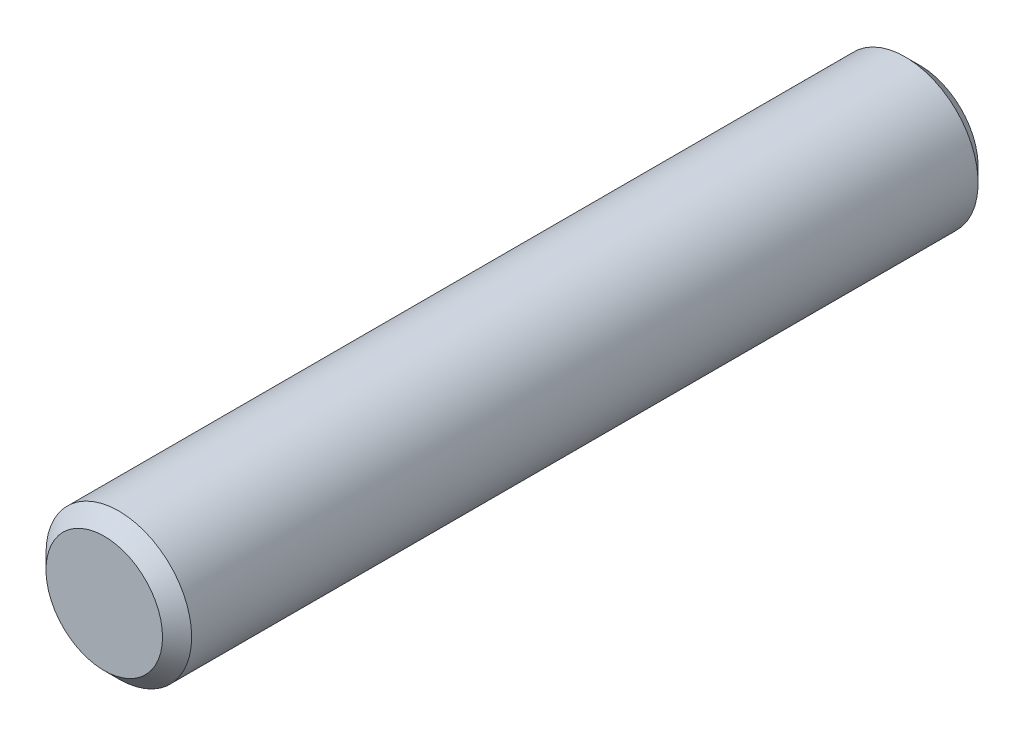
SolidWorks part; units mm, degrees
ref_plane "Plano frontal" through (0, 0, 0) normal (0, 0, 1) x (1, 0, 0)
ref_plane "Plano superior" through (0, 0, 0) normal (0, 1, 0) x (1, 0, 0)
ref_plane "Plano direito" through (0, 0, 0) normal (1, 0, 0) x (0, 0, -1)
ref_plane "Plano1" through (0, 0, 0) normal (0, -1, 0) x (1, 0, 0)
sketch "Esboço1" plane through (0, 0, 0) normal (0, -1, 0) x (1, 0, 0)
  line L0 (2.5, 28) -> (0, 28)
  line L1 (0, 28) -> (0, 0)
  line L2 (0, 0) -> (2.5, 0)
  line L12 (0, 28) -> (0, 0) construction
  line L17 (2.5, 0) -> (2.5, 28)
  dimension "D1" = 28
revolve "Revolução1" add sketch "Esboço1" angle 360 about L12
chamfer "Chanfro1" distance 0.5 angle 45 2 edges at (-2.5, 0, 28) (-2.5, 0, 0)
